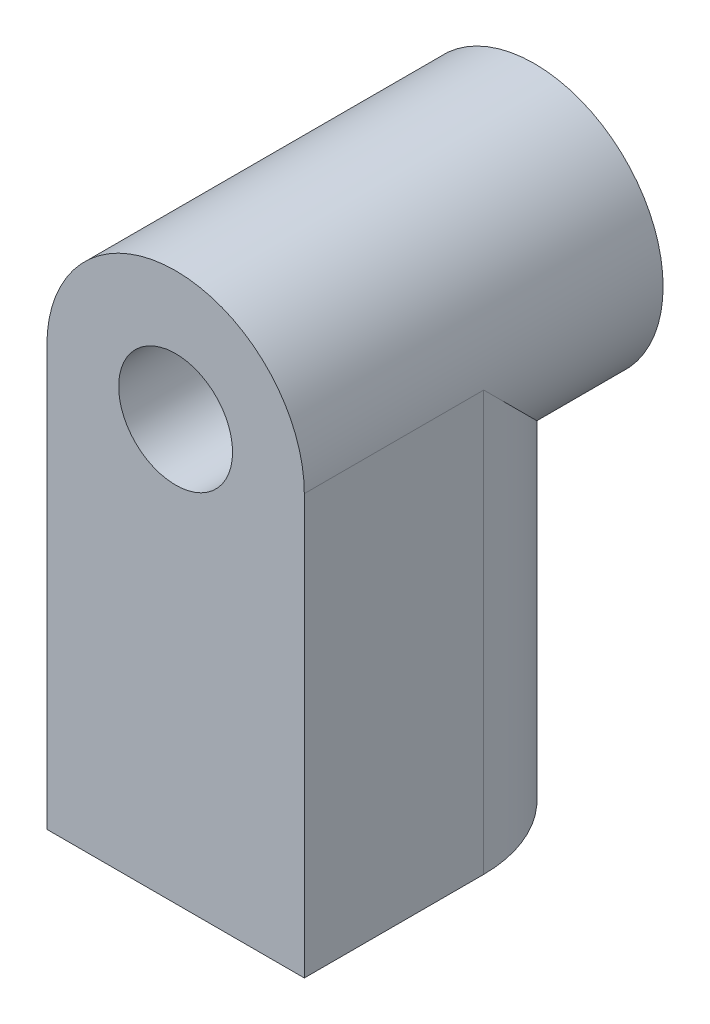
SolidWorks part; units mm, degrees
ref_plane "Front Plane" through (0, 0, 0) normal (0, 0, 1) x (1, 0, 0)
ref_plane "Top Plane" through (0, 0, 0) normal (0, 1, 0) x (1, 0, 0)
ref_plane "Right Plane" through (0, 0, 0) normal (1, 0, 0) x (0, 0, -1)
sketch "Sketch1" plane through (0, 0, 0) normal (0, 0, 1) x (1, 0, 0)
  circle A0 centre (0, 0) radius 1.5875
  circle A1 centre (0, 0) radius 3.5875
  dimension "D1" = 3.175
  dimension "D2" = 2
extrude "Boss-Extrude1" add sketch "Sketch1" along normal blind 10
ref_plane "Plane1" through (0, -1.692, 0) normal (0, 1, 0) x (1, 0, 0)
sketch "Sketch2" plane through (0, -1.692, 0) normal (0, 1, 0) x (1, 0, 0)
  line L0 (-3.5875, -5) -> (-3.5875, -10)
  line L1 (-3.5875, -10) -> (3.5875, -10)
  line L2 (3.5875, -10) -> (3.5875, -5)
  circle A0 centre (0, -5) radius 1.5875
  arc A1 (3.5875, -5) -> (-3.5875, -5) centre (0, -5) ccw
  dimension "D1" = 3.175
  dimension "D2" = 2
extrude "Boss-Extrude2" add sketch "Sketch2" against normal blind 10
sketch "Sketch3" plane through (0, -1.692, 0) normal (0, 1, 0) x (1, 0, 0)
  line L0 (-3.5875, -10) -> (-3.5875, -5)
  line L1 (-3.5875, -10) -> (-3.1635, -10)
  line L2 (-3.1635, -10) -> (-3.1635, -3.308)
  line L3 (0, -10) -> (0, -6.8309) construction
  line L4 (-3.5875, -10) -> (3.5875, -10) construction
  line L5 (3.1635, -10) -> (3.1635, -3.308)
  line L6 (3.5875, -10) -> (3.1635, -10)
  line L7 (3.5875, -10) -> (3.5875, -5)
  arc A0 (-3.1635, -3.308) -> (-3.5875, -5) centre (0, -5) ccw
  arc A1 (3.1635, -3.308) -> (3.5875, -5) centre (0, -5) cw
extrude "Boss-Extrude3" add sketch "Sketch3" along normal up to next
